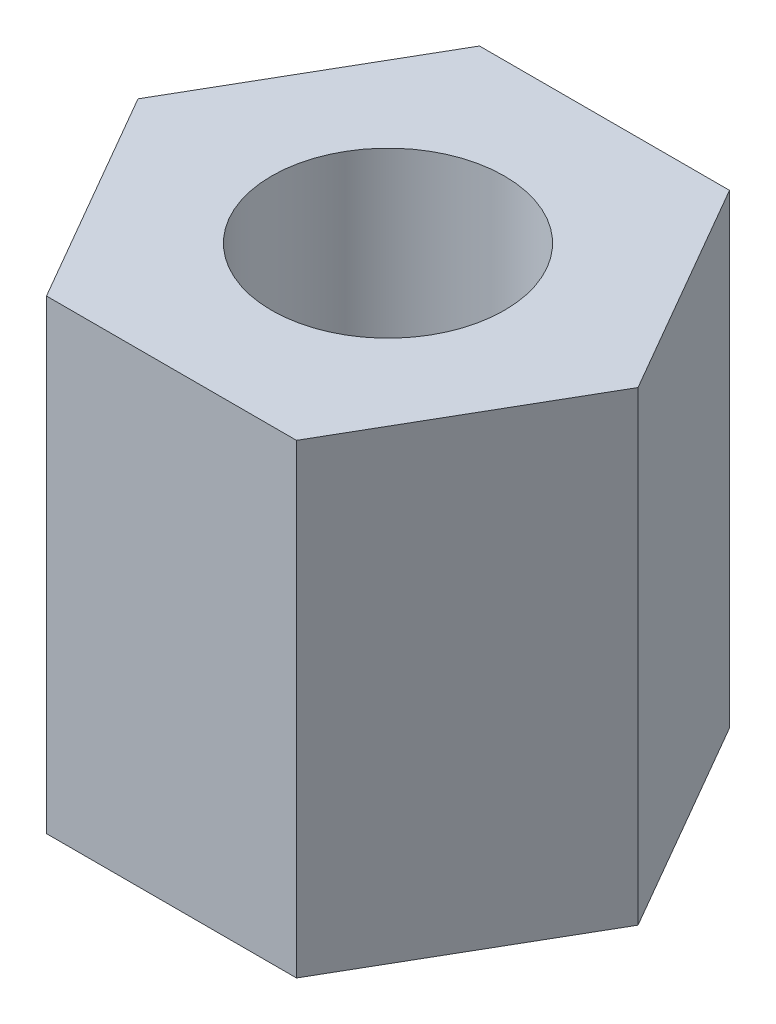
SolidWorks part; units mm, degrees
material "黄铜"
ref_plane "前视基准面" through (0, 0, 0) normal (0, 0, 1) x (1, 0, 0)
ref_plane "上视基准面" through (0, 0, 0) normal (0, 1, 0) x (1, 0, 0)
ref_plane "右视基准面" through (0, 0, 0) normal (1, 0, 0) x (0, 0, -1)
sketch "草图1" plane through (0, 0, 0) normal (0, 1, 0) x (1, 0, 0)
  line L1 (2.6847, 0) -> (1.3423, 2.325)
  line L2 (1.3423, 2.325) -> (-1.3423, 2.325)
  line L3 (-1.3423, 2.325) -> (-2.6847, 0)
  line L4 (-2.6847, 0) -> (-1.3423, -2.325)
  line L5 (-1.3423, -2.325) -> (1.3423, -2.325)
  line L6 (1.3423, -2.325) -> (2.6847, 0)
  circle A0 centre (0, 0) radius 2.325 construction
extrude "凸台-拉伸1" add sketch "草图1" along normal mid plane 5
hole_wizard "M3 螺纹孔1" positions "草图3" profile "草图2" tap size "M3" standard "GB"
sketch "草图3" plane through (0, -2.5, 0) normal (0, -1, 0) x (-1, 0, 0)
  point P0 (0, 0)
sketch "草图2" plane through (0, -2.5, 0) normal (1, 0, 0) x (0, 0, -1)
  line L0 (0, 0) -> (0, 8.2511)
  line L1 (0, 8.2511) -> (1.25, 7.5)
  line L2 (1.25, 7.5) -> (1.25, 0)
  line L5 (1.25, 0) -> (0, 0)
  line L10 (0, 8.2511) -> (-1.25, 7.5) construction
  line L11 (0, -6.35) -> (0, 107.95) construction
  dimension "螺纹孔钻头直径" = 2.5
  dimension "螺纹孔钻头深度" = 7.5
  dimension "导头角度" = 118
cosmetic thread "孔螺蚊线1" parameters "D1"=5, "D2"=3
mirror "镜向1" about plane through (0, 0, 0) normal (0, 1, 0) of "M3 螺纹孔1"
equation "\"高度\"= 5"
equation "\"对边距离\"= 4.65"
equation "\"D1@草图1\"=\"对边距离\""
equation "\"D1@凸台-拉伸1\"=\"高度\""
